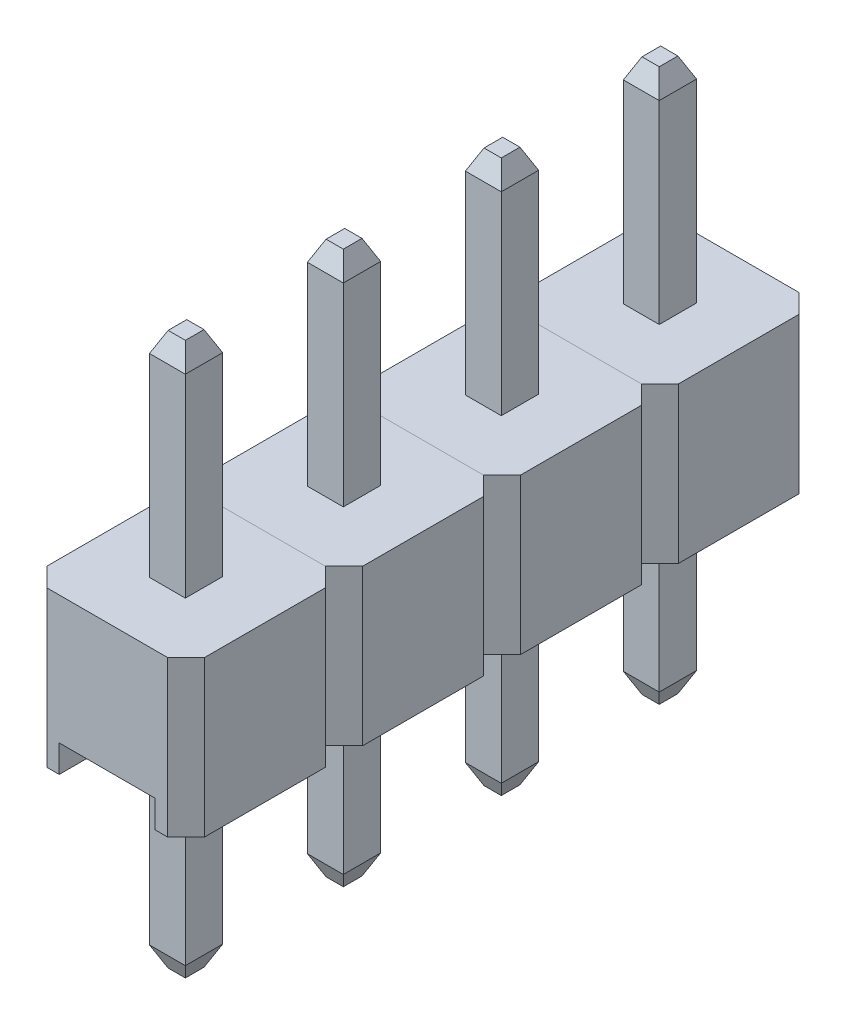
SolidWorks part; units mm, degrees
material "Latón"
ref_plane "Alzado" through (0, 0, 0) normal (0, 0, 1) x (1, 0, 0)
ref_plane "Planta" through (0, 0, 0) normal (0, 1, 0) x (1, 0, 0)
ref_plane "Vista lateral" through (0, 0, 0) normal (1, 0, 0) x (0, 0, -1)
sketch "Croquis1" plane through (0, 0, 0) normal (0, 1, 0) x (1, 0, 0)
  line L0 (0.3, 0) -> (2.24, 0)
  line L1 (2.54, 0.3) -> (2.54, 2.24)
  line L2 (2.24, 2.54) -> (0.3, 2.54)
  line L3 (0, 2.24) -> (0, 0.3)
  line L4 (0.3, 2.54) -> (0, 2.24)
  line L5 (2.54, 2.24) -> (2.24, 2.54)
  line L6 (2.24, 0) -> (2.54, 0.3)
  line L7 (0, 0.3) -> (0.3, 0)
  point P0 (0, 0)
  point P1 (2.54, 0)
  point P2 (0, 2.54)
  point P3 (2.54, 2.54)
  dimension "D1" = 0.3
  dimension "D2" = 45
  dimension "D3" = 0.3
  dimension "D4" = 45
  dimension "D5" = 0.3
  dimension "D6" = 45
  dimension "D7" = 0.3
  dimension "D8" = 45
extrude "Cuerpo Plástico" add sketch "Croquis1" along normal blind 2.5
sketch "Croquis2" plane through (0, 0, 0) normal (0, -1, 0) x (1, 0, 0)
  line L0 (0.5, 0) -> (0.5, -2.54)
  line L3 (0, -2.24) -> (0, -0.3) construction
  line L4 (2.04, 0) -> (2.04, -2.54)
  line L7 (2.54, -0.3) -> (2.54, -2.24) construction
  line L8 (0.5, 0) -> (2.04, 0)
  line L9 (0.5, -2.54) -> (2.04, -2.54)
  dimension "D1" = 0.5
  dimension "D2" = 0.5
  dimension "D3" = 1.54
extrude "Ranura" cut sketch "Croquis2" against normal blind 0.44
sketch "Croquis3" plane through (0, 2.5, 0) normal (0, 1, 0) x (1, 0, 0)
  line L0 (0.9812, 1.57) -> (1.5588, 1.57)
  line L1 (1.27, 2.54) -> (1.27, 1.57) construction
  line L2 (2.24, 2.54) -> (0.3, 2.54) construction
  line L3 (1.5588, 1.57) -> (1.5588, 0.97)
  line L4 (1.5588, 0.97) -> (0.9812, 0.97)
  line L5 (0.9812, 0.97) -> (0.9812, 1.57)
  line L6 (0, 1.27) -> (0.9812, 1.27) construction
  line L7 (0, 2.24) -> (0, 0.3) construction
  dimension "D1" = 0.6
extrude "Pin" add sketch "Croquis3" along normal blind 3.44 and the other way blind 5.44
chamfer "Chaflán1" distance 0.15 angle 65 4 edges at (1.27, 5.94, -1.57) (1.5588, 5.94, -1.27) (1.27, 5.94, -0.97) (0.9812, 5.94, -1.27)
chamfer "Chaflán2" distance 0.15 angle 65 4 edges at (1.27, -2.94, -0.97) (1.5588, -2.94, -1.27) (1.27, -2.94, -1.57) (0.9812, -2.94, -1.27)
sketch "Dirección" plane through (0, 0, 0) normal (-1, 0, 0) x (0, 0, 1)
  line L0 (-2.24, 1.25) -> (-0.3, 1.25) construction
  line L1 (-2.24, 2.5) -> (-2.24, 0) construction
  line L2 (-0.3, 2.5) -> (-0.3, 0) construction
sketch "Dirección 2" plane through (0, 0, -2.54) normal (0, 0, -1) x (-1, 0, 0)
  line L0 (-2.24, 1.25) -> (-0.3, 1.25) construction
  line L1 (-2.24, 2.5) -> (-2.24, 0) construction
  line L2 (-0.3, 2.5) -> (-0.3, 0) construction
pattern_linear "Matriz" count 4 spacing 2.54 along (0, 0, 1) of bodies 103
